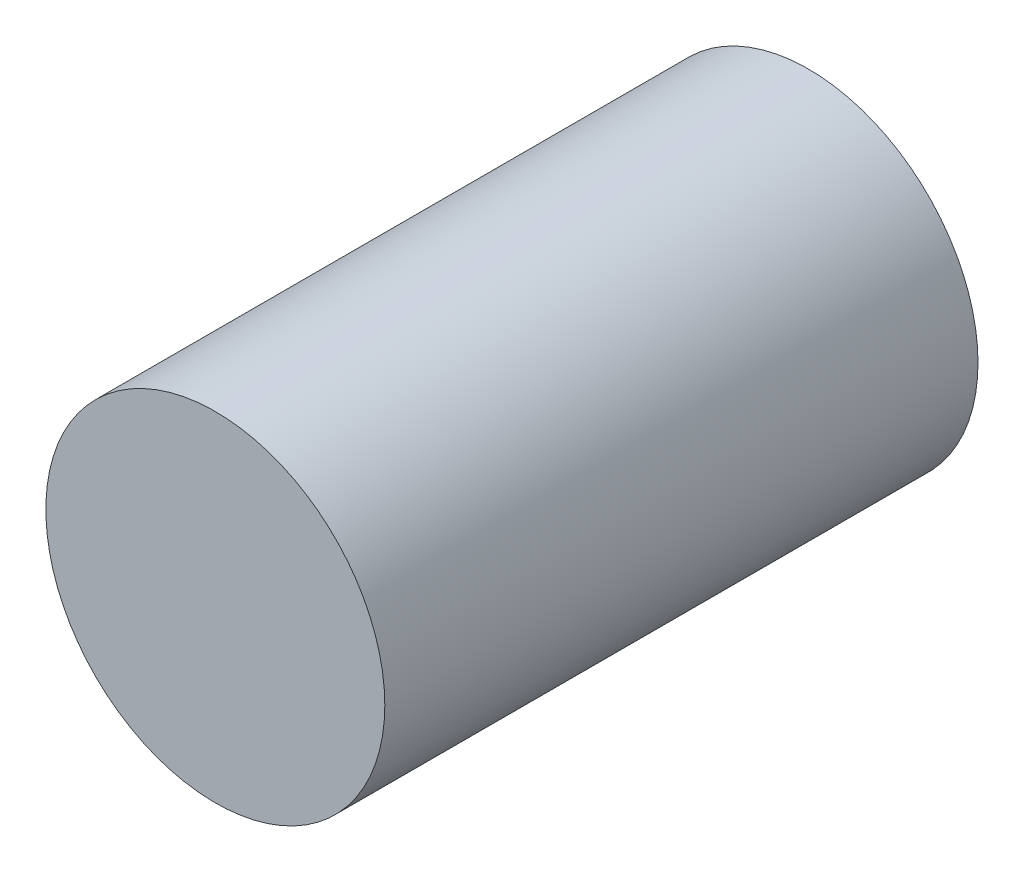
SolidWorks part; units mm, degrees
ref_plane "Front Plane" through (0, 0, 0) normal (0, 0, 1) x (1, 0, 0)
ref_plane "Top Plane" through (0, 0, 0) normal (0, 1, 0) x (1, 0, 0)
ref_plane "Right Plane" through (0, 0, 0) normal (1, 0, 0) x (0, 0, -1)
sketch "Sketch1" plane through (0, 0, 0) normal (0, 0, 1) x (1, 0, 0)
  circle A0 centre (-8.2193, 0) radius 5.08
extrude "Boss-Extrude1" add sketch "Sketch1" along normal blind 17.78
